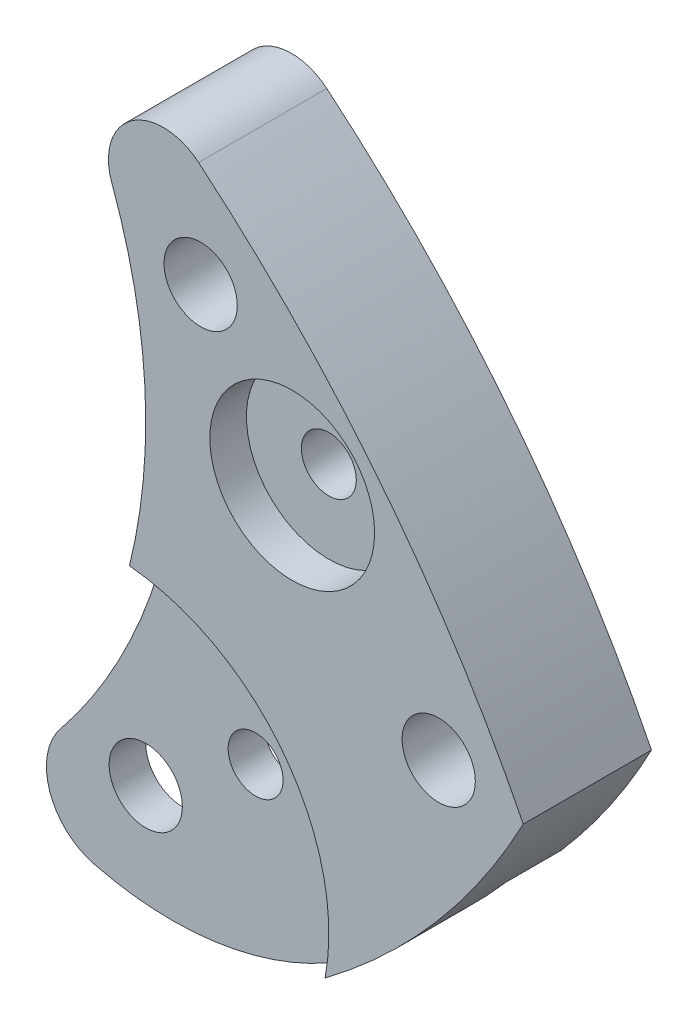
SolidWorks part; units mm, degrees
ref_plane "Alzado" through (0, 0, 0) normal (0, 0, 1) x (1, 0, 0)
ref_plane "Planta" through (0, 0, 0) normal (0, 1, 0) x (1, 0, 0)
ref_plane "Vista lateral" through (0, 0, 0) normal (1, 0, 0) x (0, 0, -1)
sketch "Croquis1" plane through (0, 0, 0) normal (0, 0, 1) x (1, 0, 0)
  arc A0 (8.8346, 5.2875) -> (10.0374, 12.5933) centre (3, 10) ccw
  arc A1 (10.0374, 12.5933) -> (11.2221, 13.4282) centre (10.7411, 12.8527) cw
  arc A2 (15.6548, 7.8217) -> (11.2221, 13.4282) centre (0, 0) ccw
  arc A3 (8.8346, 5.2875) -> (9.2876, 3.9214) centre (9.5, 4.75) ccw
  arc A4 (9.2876, 3.9214) -> (12.949, 4.6493) centre (10.3594, 8.103) ccw
  arc A5 (12.949, 4.6493) -> (15.6548, 7.8217) centre (7.25, 12.25) ccw
  circle A6 centre (10, 5.2) radius 0.5
  circle A7 centre (10, 5.2) radius 3 construction
  circle A8 centre (11.25, 12) radius 0.5
  circle A9 centre (14.5, 8) radius 0.5
  dimension "D3" = 10
  dimension "D4" = 9.5
  dimension "D5" = 7.5
  dimension "D9" = 0.75
  dimension "D10" = 17.5
  dimension "D11" = 1
  dimension "D14" = 6
  dimension "D15" = 1
  dimension "D16" = 1
  dimension "D1" = 9.5
  dimension "D2" = 4.75
  dimension "D6" = 3
  dimension "D7" = 7.25
  dimension "D8" = 12.25
  dimension "D12" = 10
  dimension "D13" = 5.2
  dimension "D17" = 14.5
  dimension "D18" = 8
  dimension "D19" = 12
  dimension "D20" = 11.25
extrude "Saliente-Extruir1" add sketch "Croquis1" along normal blind 1.75
sketch "Croquis3" plane through (0, 0, 0) normal (0, 0, -1) x (-1, 0, 0)
  circle A0 centre (-10, 5.2) radius 4.5
  circle A2 centre (-10, 5.2) radius 0.5 construction
  dimension "D1" = 9
extrude "Cortar-Extruir2" cut sketch "Croquis3" against normal blind 0.75
sketch "Croquis4" plane through (0, 0, 0) normal (0, 0, -1) x (-1, 0, 0)
  arc A1 (-10.0374, 12.5933) -> (-11.2221, 13.4282) centre (-10.7411, 12.8527) ccw construction
  arc A2 (-10.272, 12.6798) -> (-10.7426, 9.662) centre (-3, 10) ccw
  arc A3 (-10.0669, 13.1813) -> (-10.7416, 9.6385) centre (-3, 10) ccw
  arc A4 (-10.0374, 12.5933) -> (-10.4929, 9.6729) centre (-3, 10) ccw construction
  arc A5 (-10.0374, 12.5933) -> (-10.0669, 13.1813) centre (-10.7411, 12.8527) ccw
  arc A6 (-10.0374, 12.5933) -> (-10.4929, 9.6729) centre (-3, 10) ccw
  arc A7 (-10.4929, 9.6729) -> (-14.4242, 6.0226) centre (-10, 5.2) ccw construction
  arc A8 (-10.4929, 9.6729) -> (-10.7416, 9.6385) centre (-10, 5.2) ccw
  dimension "D1" = 0.25
extrude "Cortar-Extruir3" cut sketch "Croquis4" against normal up to surface (0.75 mm away) up to face at (9.5, 5.2, 0.75)
sketch "Croquis5" plane through (0, 0, 1.75) normal (0, 0, 1) x (1, 0, 0)
  circle A0 centre (12.5, 10.25) radius 1.125
  dimension "D1" = 2.25
  dimension "D2" = 10.25
  dimension "D3" = 12.5
extrude "Cortar-Extruir4" cut sketch "Croquis5" against normal blind 0.5
hole_wizard "Taladro roscado M1x0.251" positions "Croquis7" profile "Croquis6" tap size "M1x0.25" standard "KS" end condition through all
sketch "Croquis7" plane through (0, 0, 1.25) normal (0, 0, 1) x (1, 0, 0)
  circle A0 centre (12.5, 10.25) radius 1.125 construction
  point P0 (12.5, 10.25)
sketch "Croquis6" plane through (12.5, 10.25, 1.25) normal (1, 0, 0) x (0, -1, 0)
  line L0 (0, 0) -> (0, 1.25)
  line L1 (0, 1.25) -> (0.375, 1.25)
  line L2 (0.375, 1.25) -> (0.375, 0)
  line L5 (0.375, 0) -> (0, 0)
  line L11 (0, -6.35) -> (0, 107.95) construction
  dimension "Diámetro de perforador para roscar hasta el siguiente" = 0.75
  dimension "Profundidad de perforador para roscar hasta el siguiente" = 1.25
cosmetic thread "Rosca de taladro1"
sketch "Croquis8" plane through (0, 0, 1.75) normal (0, 0, 1) x (1, 0, 0)
  circle A0 centre (10, 5.2) radius 3
  dimension "D1" = 6
extrude "Cortar-Extruir5" cut sketch "Croquis8" against normal blind 0.5
hole_wizard "Taladro roscado M1x0.252" positions "Croquis12" profile "Croquis11" tap size "M1x0.25" standard "KS"
sketch "Croquis12" plane through (0, 0, 1.25) normal (0, 0, 1) x (1, 0, 0)
  circle A1 centre (10, 5.2) radius 0.5 construction
  point P0 (11.5, 6.2)
  dimension "D1" = 1.5
  dimension "D2" = 1
sketch "Croquis11" plane through (11.5, 6.2, 1.25) normal (1, 0, 0) x (0, -1, 0)
  line L0 (0, 0) -> (0, 2.2253)
  line L1 (0, 2.2253) -> (0.375, 2)
  line L2 (0.375, 2) -> (0.375, 0)
  line L5 (0.375, 0) -> (0, 0)
  line L10 (0, 2.2253) -> (-0.375, 2) construction
  line L11 (0, -6.35) -> (0, 107.95) construction
  dimension "Diámetro de perforador para roscar" = 0.75
  dimension "Profundidad de perforador para roscar" = 2
  dimension "Ángulo de perforador" = 118
cosmetic thread "Rosca de taladro2"
